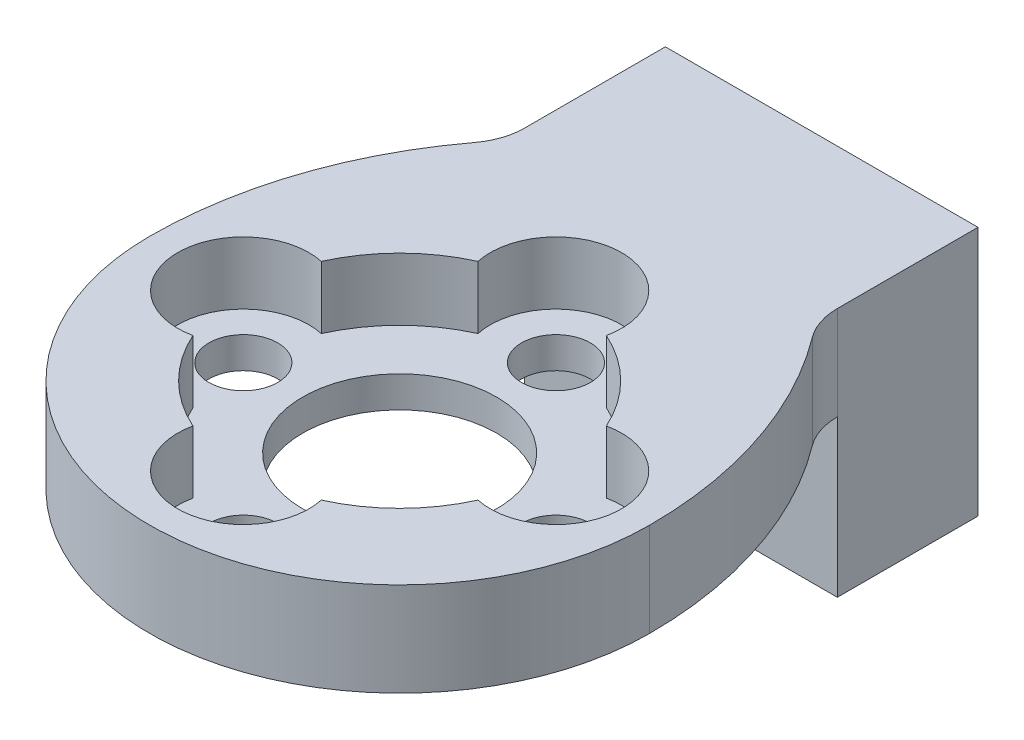
SolidWorks part; units mm, degrees
ref_plane "Front Plane" through (0, 0, 0) normal (0, 0, 1) x (1, 0, 0)
ref_plane "Top Plane" through (0, 0, 0) normal (0, 1, 0) x (1, 0, 0)
ref_plane "Right Plane" through (0, 0, 0) normal (1, 0, 0) x (0, 0, -1)
ref_plane "Plane1" through (0, 3, 0) normal (0, 1, 0) x (1, 0, 0)
sketch "Sketch1" plane through (0, 3, 0) normal (0, 1, 0) x (1, 0, 0)
  line L0 (5, -5.1934) -> (5, 0)
  line L1 (5, 0) -> (-5, 0)
  line L2 (-5, 0) -> (-5, -5.1934)
  arc A0 (-5, -5.1934) -> (-8, -13.5) centre (5, -13.5) ccw
  arc A1 (-8, -13.5) -> (8, -13.5) centre (0, -13.5) ccw
  arc A2 (8, -13.5) -> (5, -5.1934) centre (-5, -13.5) ccw
extrude "Boss-Extrude1" add sketch "Sketch1" against normal blind 3
sketch "Sketch2" plane through (0, 0, 0) normal (0, -1, 0) x (1, 0, 0)
  line L0 (-5, 0) -> (-5, 4.5)
  line L1 (-5, 4.5) -> (5, 4.5)
  line L2 (5, 4.5) -> (5, 0)
  line L3 (5, 0) -> (-5, 0)
extrude "Boss-Extrude2" add sketch "Sketch2" along normal blind 5
sketch "Sketch3" plane through (0, 3, 0) normal (0, 1, 0) x (-1, 0, 0)
  arc A0 (-2.0532, 18.059) -> (-4.559, 15.5532) centre (0, 13.5) ccw
  arc A1 (-4.559, 15.5532) -> (-4.559, 11.4468) centre (-5, 13.5) ccw
  arc A2 (-4.559, 11.4468) -> (-2.0532, 8.941) centre (0, 13.5) ccw
  arc A3 (-2.0532, 8.941) -> (2.0532, 8.941) centre (0, 8.5) ccw
  arc A4 (2.0532, 8.941) -> (4.559, 11.4468) centre (0, 13.5) ccw
  arc A5 (4.559, 11.4468) -> (4.559, 15.5532) centre (5, 13.5) ccw
  arc A6 (4.559, 15.5532) -> (2.0532, 18.059) centre (0, 13.5) ccw
  arc A7 (2.0532, 18.059) -> (-2.0532, 18.059) centre (0, 18.5) ccw
extrude "Cut-Extrude1" cut sketch "Sketch3" against normal blind 2
hole_wizard "Ø2.2 (2.2) Diameter Hole1" positions "Sketch5" profile "Sketch4" hole size "Ø2.2" standard "ANSI Metric"
sketch "Sketch5" plane through (0, 1, 0) normal (0, 1, 0) x (1, 0, 0)
  point P0 (-5, -13.5)
sketch "Sketch4" plane through (-5, 1, 13.5) normal (1, 0, 0) x (0, 0, 1)
  line L0 (0, 0) -> (0, 6)
  line L1 (0, 6) -> (1.1, 6)
  line L2 (1.1, 6) -> (1.1, 0)
  line L5 (1.1, 0) -> (0, 0)
  line L11 (0, -6.35) -> (0, 107.95) construction
  dimension "Thru Hole Dia." = 2.2
  dimension "Thru Hole Depth" = 6
hole_wizard "Ø6.2 (6.2) Diameter Hole1" positions "Sketch7" profile "Sketch6" hole size "Ø6.2" standard "ANSI Metric"
sketch "Sketch7" plane through (0, 0, 0) normal (0, -1, 0) x (-1, 0, 0)
  point P0 (0, -13.5)
sketch "Sketch6" plane through (0, 0, 13.5) normal (1, 0, 0) x (0, 0, -1)
  line L0 (0, 0) -> (0, 3)
  line L1 (0, 3) -> (3.1, 3)
  line L2 (3.1, 3) -> (3.1, 0)
  line L5 (3.1, 0) -> (0, 0)
  line L11 (0, -6.35) -> (0, 107.95) construction
  dimension "Thru Hole Dia." = 6.2
  dimension "Thru Hole Depth" = 3
hole_wizard "Ø2.2 (2.2) Diameter Hole2" positions "Sketch9" profile "Sketch8" hole size "Ø2.2" standard "ANSI Metric"
sketch "Sketch9" plane through (0, 0, 0) normal (0, -1, 0) x (-1, 0, 0)
  point P0 (0, -8.5)
  point P1 (-5, -13.5)
  point P2 (0, -18.5)
sketch "Sketch8" plane through (0, 0, 8.5) normal (1, 0, 0) x (0, 0, -1)
  line L0 (0, 0) -> (0, 3)
  line L1 (0, 3) -> (1.1, 3)
  line L2 (1.1, 3) -> (1.1, 0)
  line L5 (1.1, 0) -> (0, 0)
  line L11 (0, -6.35) -> (0, 107.95) construction
  dimension "Thru Hole Dia." = 2.2
  dimension "Thru Hole Depth" = 3
hole_wizard "Ø2.5 (2.5) Diameter Hole1" positions "Sketch11" profile "Sketch10" hole size "Ø2.5" standard "ANSI Metric"
sketch "Sketch11" plane through (0, 0, 0) normal (0, 0, -1) x (-1, 0, 0)
  point P0 (-1.5, -2)
sketch "Sketch10" plane through (1.5, -2, 0) normal (1, 0, 0) x (0, 1, 0)
  line L0 (0, 0) -> (0, 21.5)
  line L1 (0, 21.5) -> (1.25, 21.5)
  line L2 (1.25, 21.5) -> (1.25, 0)
  line L5 (1.25, 0) -> (0, 0)
  line L11 (0, -6.35) -> (0, 107.95) construction
  dimension "Thru Hole Dia." = 2.5
  dimension "Thru Hole Depth" = 21.5
hole_wizard "Ø1.6 (1.6) Diameter Hole1" positions "Sketch13" profile "Sketch12" hole size "Ø1.6" standard "ANSI Metric"
sketch "Sketch13" plane through (0, 0, 0) normal (0, 0, -1) x (-1, 0, 0)
  point P0 (3, 1)
sketch "Sketch12" plane through (-3, 1, 0) normal (1, 0, 0) x (0, 1, 0)
  line L0 (0, 0) -> (0, 4.4807)
  line L1 (0, 4.4807) -> (0.8, 4)
  line L2 (0.8, 4) -> (0.8, 0)
  line L5 (0.8, 0) -> (0, 0)
  line L10 (0, 4.4807) -> (-0.8, 4) construction
  line L11 (0, -6.35) -> (0, 107.95) construction
  dimension "Hole Dia." = 1.6
  dimension "Hole Depth" = 4
  dimension "Drill Angle" = 118
fillet "Fillet1" radius 2 2 edges at (5, 1.5, 5.1934) (-5, 1.5, 5.1934)
